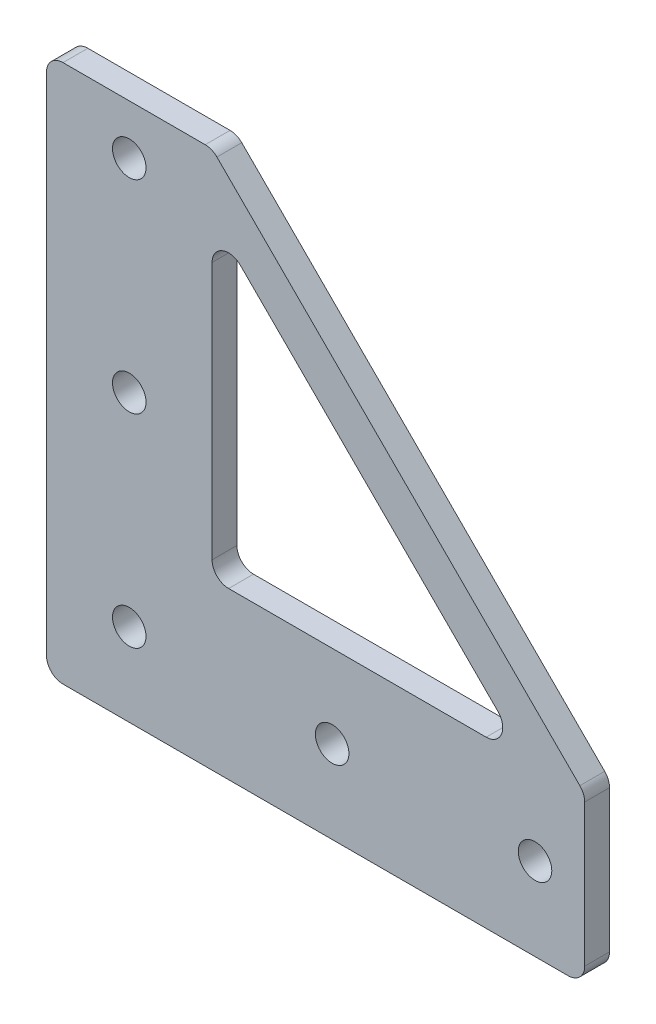
SolidWorks part; units mm, degrees
material "环氧玻璃布层压板"
ref_plane "前视基准面" through (0, 0, 0) normal (0, 0, 1) x (1, 0, 0)
ref_plane "上视基准面" through (0, 0, 0) normal (0, 1, 0) x (1, 0, 0)
ref_plane "右视基准面" through (0, 0, 0) normal (1, 0, 0) x (0, 0, -1)
sketch "草图1" plane through (0, 0, 0) normal (0, 0, 1) x (1, 0, 0)
  line L0 (0, 0) -> (0, 65)
  line L1 (0, 65) -> (20, 65)
  line L2 (20, 65) -> (20, 20)
  line L3 (20, 20) -> (65, 20)
  line L4 (65, 20) -> (65, 0)
  line L5 (65, 0) -> (0, 0)
  dimension "D1" = 20
  dimension "D2" = 20
  dimension "D3" = 65
extrude "凸台-拉伸1" add sketch "草图1" along normal blind 3
sketch "草图2" plane through (0, 0, 3) normal (0, 0, 1) x (1, 0, 0)
  line L0 (10, 59) -> (10, 10) construction
  line L1 (10, 10) -> (59, 10) construction
  line L2 (65, 20) -> (20, 20) construction
  line L3 (0, 65) -> (0, 0) construction
  line L4 (20, 65) -> (0, 65) construction
  line L5 (65, 0) -> (65, 20) construction
  circle A0 centre (10, 59) radius 2.025
  circle A1 centre (10, 34.5) radius 2.025
  circle A2 centre (10, 10) radius 2.025
  circle A3 centre (34.5, 10) radius 2.025
  circle A4 centre (59, 10) radius 2.025
  dimension "D5" = 4.05
  dimension "D1" = 10
  dimension "D2" = 10
  dimension "D3" = 6
  dimension "D4" = 6
extrude "切除-拉伸1" cut sketch "草图2" against normal blind 3
sketch "草图3" plane through (0, 0, 3) normal (0, 0, 1) x (1, 0, 0)
  line L0 (20, 65) -> (65, 20)
  line L1 (65, 20) -> (57.9289, 20)
  line L2 (65, 20) -> (20, 20) construction
  line L3 (57.9289, 20) -> (20, 57.9289)
  line L4 (20, 20) -> (20, 65) construction
  line L5 (20, 57.9289) -> (20, 65)
  dimension "D1" = 5
extrude "凸台-拉伸2" add sketch "草图3" against normal up to surface (3 mm away) up to face at (12.025, 59, 0)
fillet "圆角1" radius 2 8 edges at (20, 57.9289, 1.5) (57.9289, 20, 1.5) (0, 0, 1.5) (0, 65, 1.5) (20, 65, 1.5) (65, 0, 1.5) (65, 20, 1.5) (20, 20, 1.5)
fillet "圆角2" [suppressed] radius 2
